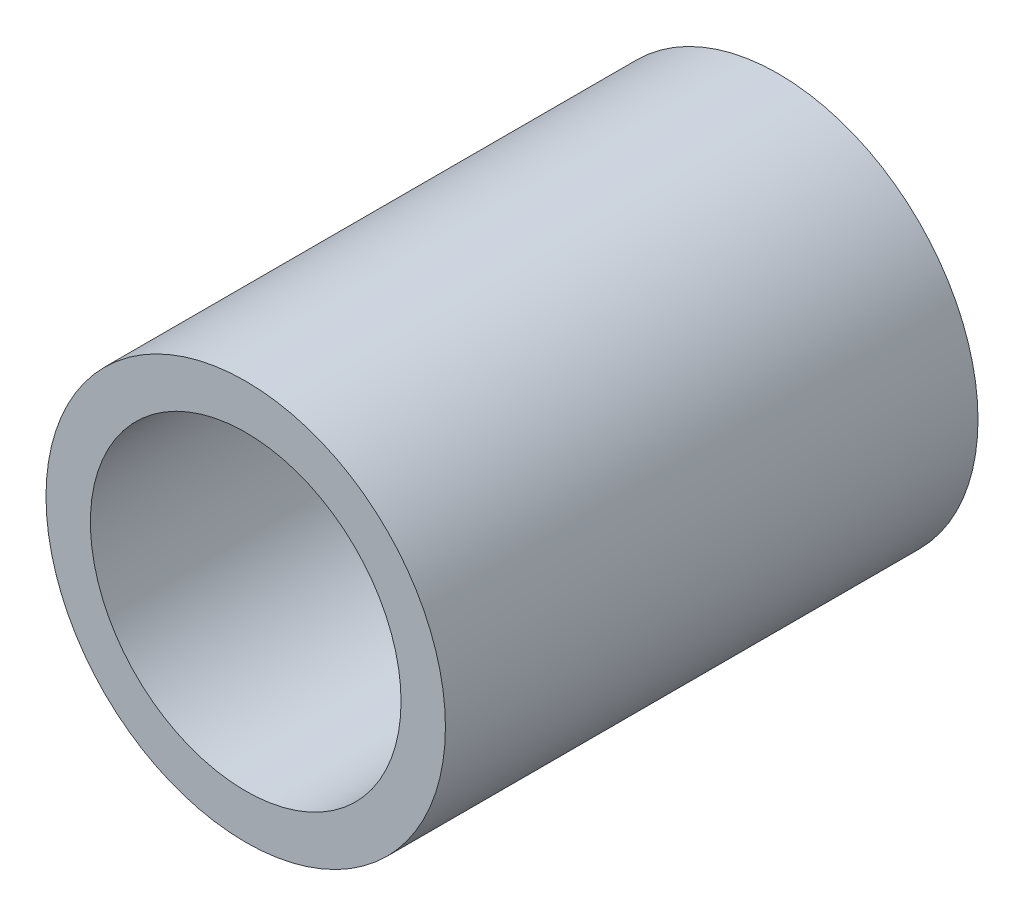
SolidWorks part; units mm, degrees
ref_plane "Front Plane" through (0, 0, 0) normal (0, 0, 1) x (1, 0, 0)
ref_plane "Top Plane" through (0, 0, 0) normal (0, 1, 0) x (1, 0, 0)
ref_plane "Right Plane" through (0, 0, 0) normal (1, 0, 0) x (0, 0, -1)
sketch "Sketch1" plane through (0, 0, 0) normal (0, 0, 1) x (1, 0, 0)
  circle A0 centre (0, 0) radius 21
  circle A1 centre (0, 0) radius 27
  dimension "D1" = 42
  dimension "D2" = 54
extrude "Boss-Extrude1" add sketch "Sketch1" along normal mid plane 72
